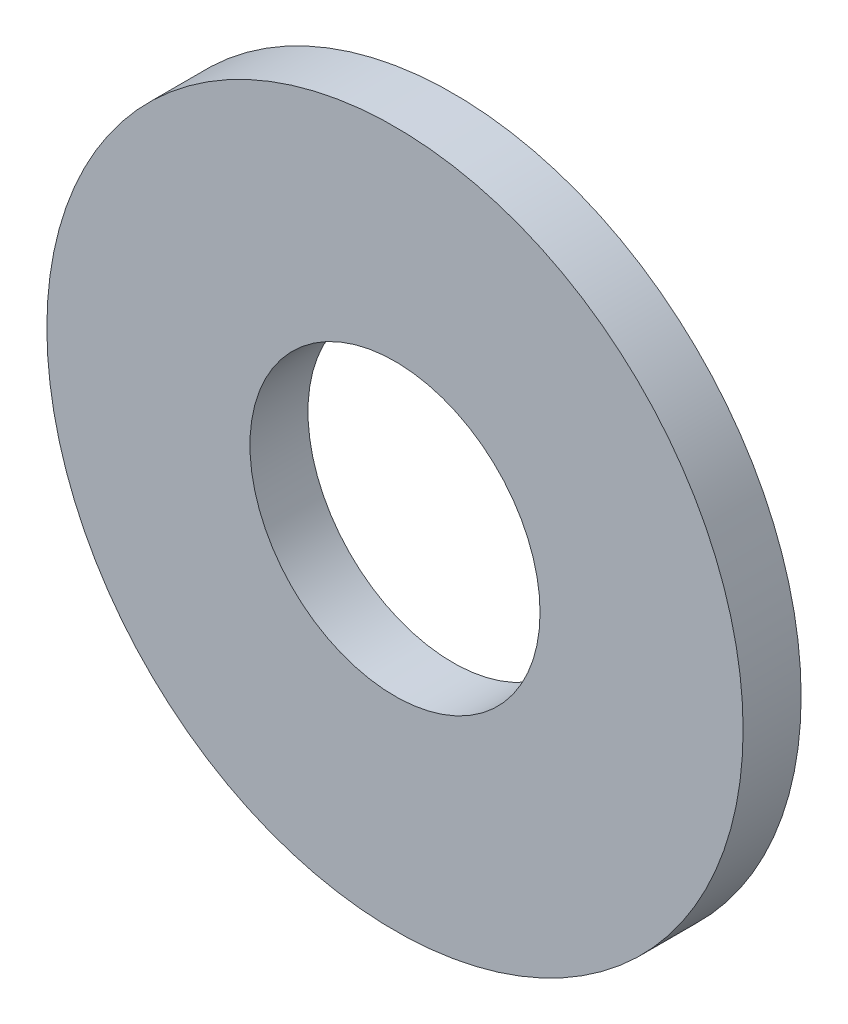
SolidWorks part; units mm, degrees
ref_plane "Plan de face" through (0, 0, 0) normal (0, 0, 1) x (1, 0, 0)
ref_plane "Plan de dessus" through (0, 0, 0) normal (0, 1, 0) x (1, 0, 0)
ref_plane "Plan de droite" through (0, 0, 0) normal (1, 0, 0) x (0, 0, -1)
sketch "Esquisse1" plane through (0, 0, 0) normal (0, 0, 1) x (1, 0, 0)
  circle A0 centre (0, 0) radius 2.5
  circle A1 centre (0, 0) radius 6
  dimension "D1" = 5
  dimension "D2" = 12
extrude "Extrusion1" add sketch "Esquisse1" along normal blind 1
